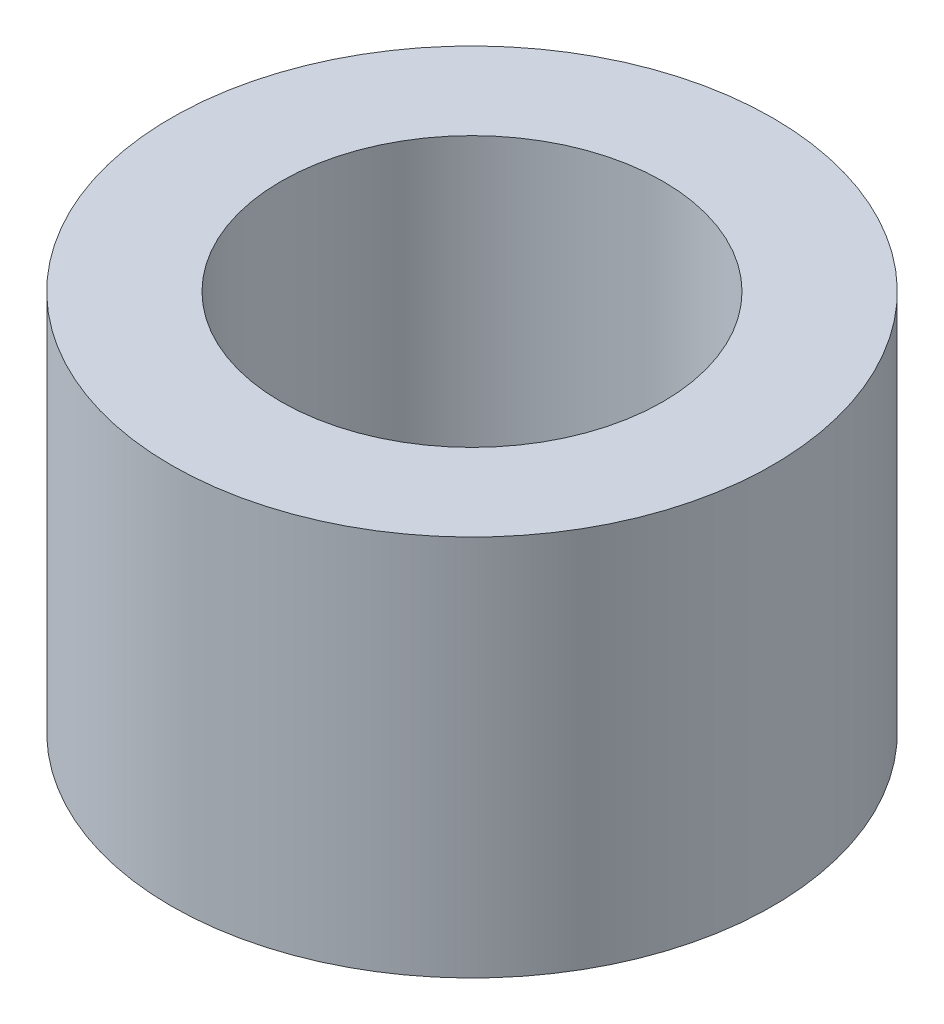
SolidWorks part; units mm, degrees
material "Brass"
ref_plane "Front Plane" through (0, 0, 0) normal (0, 0, 1) x (1, 0, 0)
ref_plane "Top Plane" through (0, 0, 0) normal (0, 1, 0) x (1, 0, 0)
ref_plane "Right Plane" through (0, 0, 0) normal (1, 0, 0) x (0, 0, -1)
sketch "Sketch1" plane through (0, 0, 0) normal (0, 0, 1) x (1, 0, 0)
  line L0 (0, 0) -> (0, 4) construction
  line L2 (2, 4) -> (2, 0)
  line L4 (2, 4) -> (3.15, 4)
  line L5 (3.15, 4) -> (3.15, 0)
  line L7 (3.15, 0) -> (2, 0)
  dimension "D1" = 4
  dimension "D2" = 2
  dimension "D3" = 3.15
revolve "Revolve1" add sketch "Sketch1" angle 360 about L0
